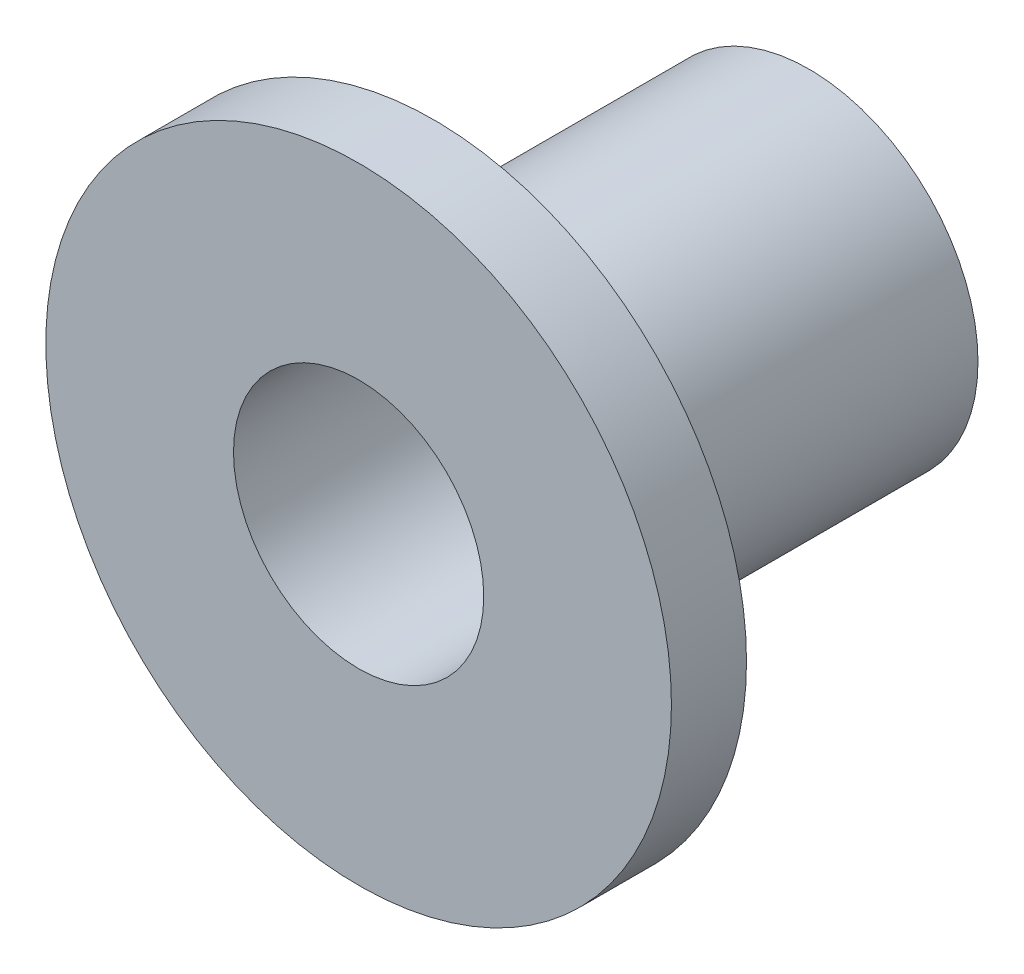
SolidWorks part; units mm, degrees
ref_plane "Front Plane" through (0, 0, 0) normal (0, 0, 1) x (1, 0, 0)
ref_plane "Top Plane" through (0, 0, 0) normal (0, 1, 0) x (1, 0, 0)
ref_plane "Right Plane" through (0, 0, 0) normal (1, 0, 0) x (0, 0, -1)
sketch "Sketch1" plane through (0, 0, 0) normal (0, 0, 1) x (1, 0, 0)
  circle A0 centre (0, 0) radius 0.3375
  dimension "D1" = 0.675
extrude "Boss-Extrude1" add sketch "Sketch1" against normal blind 0.9
sketch "Sketch2" plane through (0, 0, 0) normal (0, 0, 1) x (1, 0, 0)
  circle A0 centre (0, 0) radius 0.625
  dimension "D1" = 1.25
extrude "Boss-Extrude2" add sketch "Sketch2" against normal blind 0.15
sketch "Sketch3" plane through (0, 0, 0) normal (0, 0, 1) x (1, 0, 0)
  circle A0 centre (0, 0) radius 0.25
  dimension "D1" = 0.5
extrude "Cut-Extrude1" cut sketch "Sketch3" against normal through all
